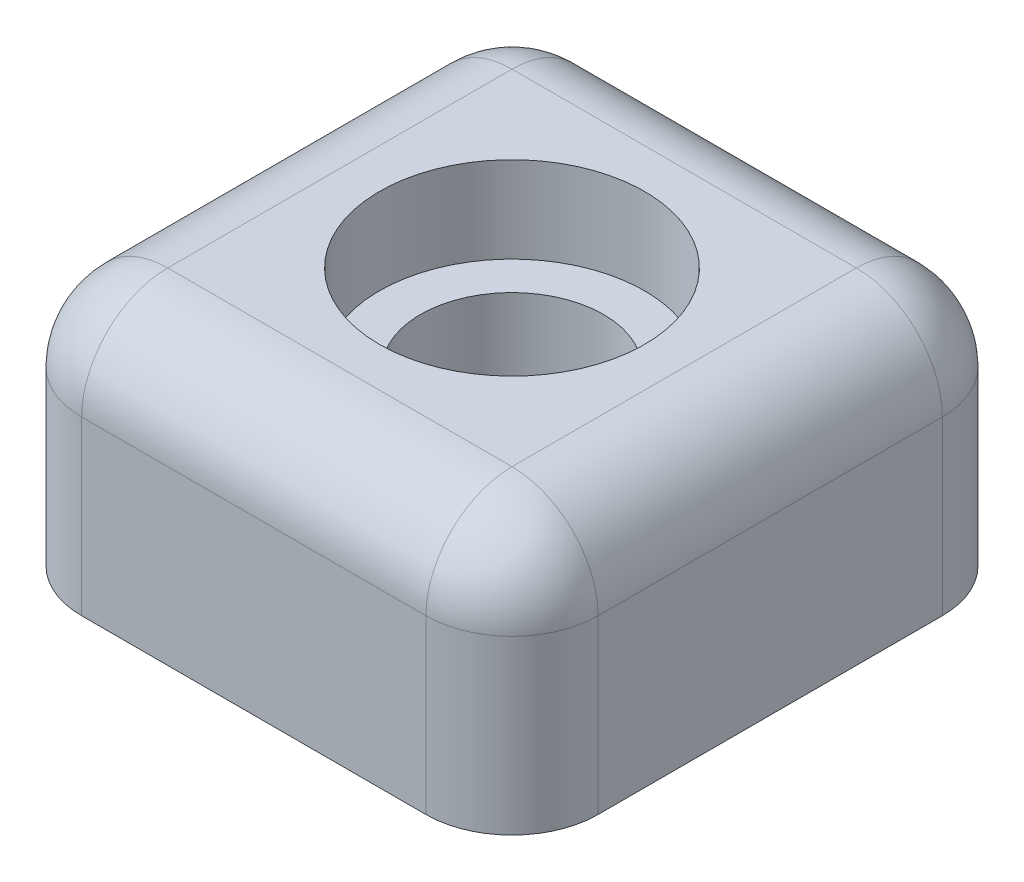
SolidWorks part; units mm, degrees
ref_plane "Front Plane" through (0, 0, 0) normal (0, 0, 1) x (1, 0, 0)
ref_plane "Top Plane" through (0, 0, 0) normal (0, 1, 0) x (1, 0, 0)
ref_plane "Right Plane" through (0, 0, 0) normal (1, 0, 0) x (0, 0, -1)
sketch "Sketch1" plane through (0, 0, 0) normal (0, 1, 0) x (1, 0, 0)
  line L1 (-9.525, -9.525) -> (9.525, -9.525)
  line L2 (-9.525, -9.525) -> (-9.525, 9.525)
  line L3 (-9.525, 9.525) -> (9.525, 9.525)
  line L4 (9.525, -9.525) -> (9.525, 9.525)
  line L5 (-9.525, -9.525) -> (9.525, 9.525) construction
  line L6 (-9.525, 9.525) -> (9.525, -9.525) construction
  circle A0 centre (0, 0) radius 4.8895
  point P0 (0, 0)
  dimension "D1" = 9.779
  dimension "D2" = 19.05
extrude "Boss-Extrude1" add sketch "Sketch1" along normal blind 3.175
sketch "Sketch3" plane through (0, 0, 0) normal (0, -1, 0) x (1, 0, 0)
  line L4 (9.525, -9.525) -> (9.525, 9.525)
  line L5 (9.525, 9.525) -> (-9.525, 9.525)
  line L6 (-9.525, 9.525) -> (-9.525, -9.525)
  line L7 (-9.525, -9.525) -> (9.525, -9.525)
  line L8 (9.525, -9.525) -> (9.525, 9.525)
  line L9 (9.525, 9.525) -> (-9.525, 9.525)
  line L10 (-9.525, 9.525) -> (-9.525, -9.525)
  line L11 (-9.525, -9.525) -> (9.525, -9.525)
  circle A0 centre (0, 0) radius 3.3782
  dimension "D2" = 6.7564
  dimension "D1" = 0
extrude "Boss-Extrude2" add sketch "Sketch3" along normal blind 3.175
sketch "Sketch4" plane through (0, -3.175, 0) normal (0, -1, 0) x (1, 0, 0)
  line L4 (-9.525, -9.525) -> (9.525, -9.525)
  line L5 (9.525, -9.525) -> (9.525, 9.525)
  line L6 (9.525, 9.525) -> (-9.525, 9.525)
  line L7 (-9.525, 9.525) -> (-9.525, -9.525)
  line L8 (-9.525, -9.525) -> (9.525, -9.525)
  line L9 (9.525, -9.525) -> (9.525, 9.525)
  line L10 (9.525, 9.525) -> (-9.525, 9.525)
  line L11 (-9.525, 9.525) -> (-9.525, -9.525)
  dimension "D1" = 0
extrude "Boss-Extrude3" add sketch "Sketch4" along normal blind 3.175
fillet "Fillet1" radius 3.175 8 edges at (-9.525, -1.5875, -9.525) (9.525, -1.5875, -9.525) (9.525, -1.5875, 9.525) (-9.525, -1.5875, 9.525) (9.525, 3.175, 0) (0, 3.175, -9.525) (-9.525, 3.175, 0) (0, 3.175, 9.525)
